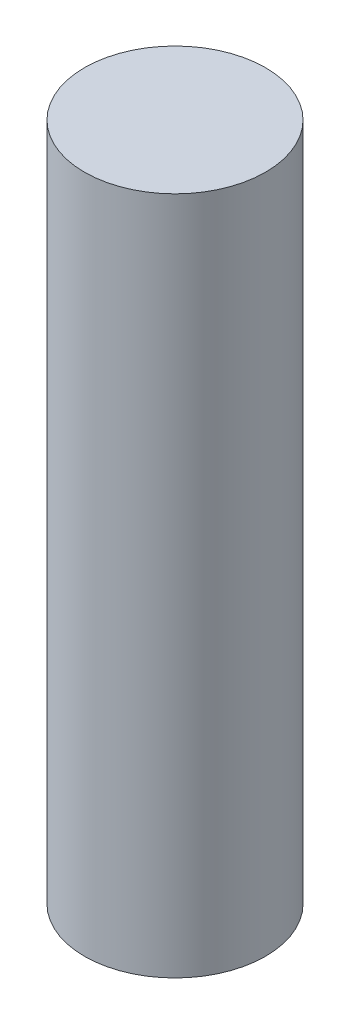
SolidWorks part; units mm, degrees
ref_plane "Front Plane" through (0, 0, 0) normal (0, 0, 1) x (1, 0, 0)
ref_plane "Top Plane" through (0, 0, 0) normal (0, 1, 0) x (1, 0, 0)
ref_plane "Right Plane" through (0, 0, 0) normal (1, 0, 0) x (0, 0, -1)
sketch "Sketch1" plane through (0, 0, 0) normal (0, 1, 0) x (1, 0, 0)
  circle A0 centre (0, 0) radius 60
  dimension "D1" = 120
extrude "Boss-Extrude1" add sketch "Sketch1" along normal blind 450 contours A0
